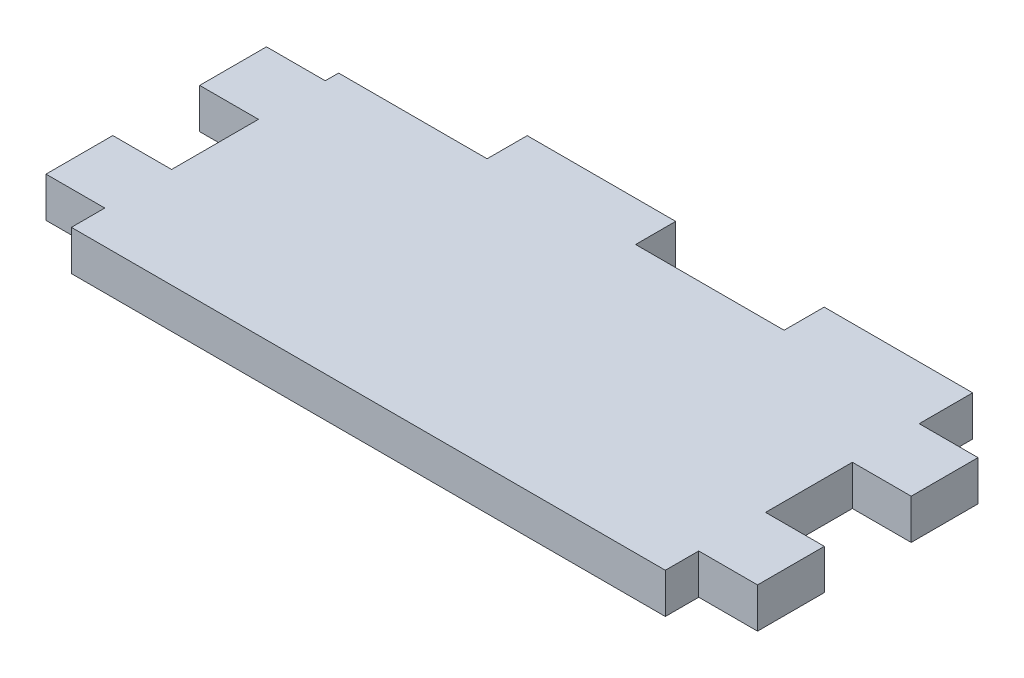
SolidWorks part; units mm, degrees
ref_plane "Front Plane" through (0, 0, 0) normal (0, 0, 1) x (1, 0, 0)
ref_plane "Top Plane" through (0, 0, 0) normal (0, 1, 0) x (1, 0, 0)
ref_plane "Right Plane" through (0, 0, 0) normal (1, 0, 0) x (0, 0, -1)
sketch "Sketch1" plane through (0, 0, 0) normal (0, 1, 0) x (1, 0, 0)
  line L0 (-22.225, -11.5) -> (22.225, 11.5) construction
  line L1 (-22.225, -11.5) -> (22.225, -11.5)
  line L2 (-22.225, -11.5) -> (-22.225, -9)
  line L3 (-22.225, 11.5) -> (22.225, 11.5)
  line L4 (22.225, -11.5) -> (22.225, -9)
  line L5 (-22.225, 7.5) -> (-22.225, 11.5)
  line L6 (-22.225, 2.5) -> (-26.625, 2.5)
  line L7 (-22.225, -4) -> (-22.225, 2.5)
  line L8 (-22.225, 7.5) -> (-26.625, 7.5)
  line L9 (-26.625, 2.5) -> (-26.625, 7.5)
  line L10 (-22.225, -9) -> (-26.625, -9)
  line L11 (22.225, -4) -> (22.225, 2.5)
  line L12 (-22.225, -4) -> (-26.625, -4)
  line L13 (-26.625, -9) -> (-26.625, -4)
  line L14 (22.225, -9) -> (26.625, -9)
  line L15 (22.225, 7.5) -> (22.225, 11.5)
  line L16 (22.225, -4) -> (26.625, -4)
  line L17 (26.625, -9) -> (26.625, -4)
  line L18 (22.225, 2.5) -> (26.625, 2.5)
  line L20 (22.225, 7.5) -> (26.625, 7.5)
  line L21 (26.625, 2.5) -> (26.625, 7.5)
  point P4 (0, 0)
  dimension "D1" = 44.45
  dimension "D2" = 23
  dimension "D3" = 4.4
  dimension "D4" = 5
  dimension "D5" = 4
  dimension "D6" = 11.5
extrude "Boss-Extrude1" add sketch "Sketch1" along normal blind 3
sketch "Sketch2" plane through (0, 3, 0) normal (0, 1, 0) x (1, 0, 0)
  line L0 (22.225, 11.5) -> (-22.225, 11.5) construction
  line L1 (-22.225, 11.5) -> (-11.1125, 11.5)
  line L2 (-22.225, 11.5) -> (-22.225, 8.5)
  line L3 (-22.225, 8.5) -> (-11.1125, 8.5)
  line L4 (-11.1125, 11.5) -> (-11.1125, 8.5)
  line L5 (0, 11.5) -> (11.1125, 11.5)
  line L6 (0, 11.5) -> (0, 8.5)
  line L7 (0, 8.5) -> (11.1125, 8.5)
  line L8 (11.1125, 11.5) -> (11.1125, 8.5)
  line L9 (-11.1125, 8.5) -> (0, 8.5) construction
  dimension "D1" = 3
extrude "Cut-Extrude1" cut sketch "Sketch2" against normal through all
